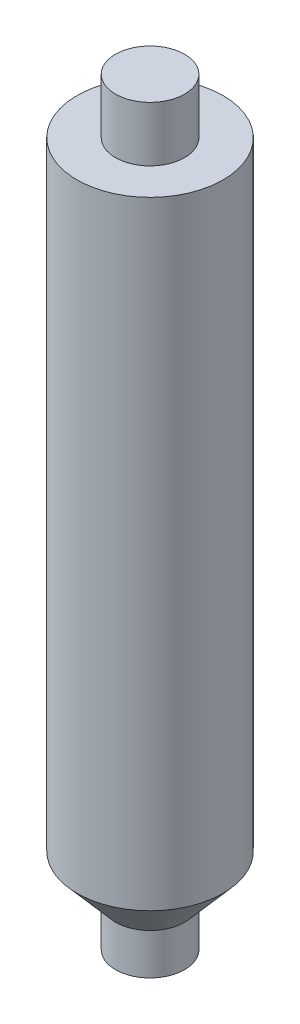
SolidWorks part; units mm, degrees
ref_plane "Front Plane" through (0, 0, 0) normal (0, 0, 1) x (1, 0, 0)
ref_plane "Top Plane" through (0, 0, 0) normal (0, 1, 0) x (1, 0, 0)
ref_plane "Right Plane" through (0, 0, 0) normal (1, 0, 0) x (0, 0, -1)
sketch "Sketch1" plane through (0, 0, 0) normal (0, 0, 1) x (1, 0, 0)
  line L0 (0, 0) -> (0, 70)
  line L1 (0, 70) -> (3.1888, 70)
  line L2 (3.1888, 70) -> (3.1888, 69.0094)
  line L3 (3.1888, 69.0094) -> (6.7437, 64.92) construction
  line L4 (6.7437, 64.92) -> (3.1888, 64.92)
  line L5 (6.7437, 64.92) -> (6.7437, 7.884)
  line L6 (6.7437, 7.884) -> (3.1888, 3.7946)
  line L7 (3.1888, 3.7946) -> (3.1888, 0)
  line L8 (3.1888, 0) -> (0, 0)
  line L9 (3.1888, 3.7946) -> (3.1888, 7.884) construction
  line L10 (3.1888, 7.884) -> (6.7437, 7.884) construction
  line L11 (3.1888, 69.0094) -> (3.1888, 64.92)
  dimension "D1" = 70
  dimension "D2" = 41
  dimension "D3" = 3.1888
  dimension "D4" = 6.7437
  dimension "D5" = 41
  dimension "D6" = 4.0894
  dimension "D7" = 4.0894
  dimension "D8" = 5.08
  dimension "D9" = 6.7437
revolve "Revolve1" add sketch "Sketch1" angle 360 about L0
